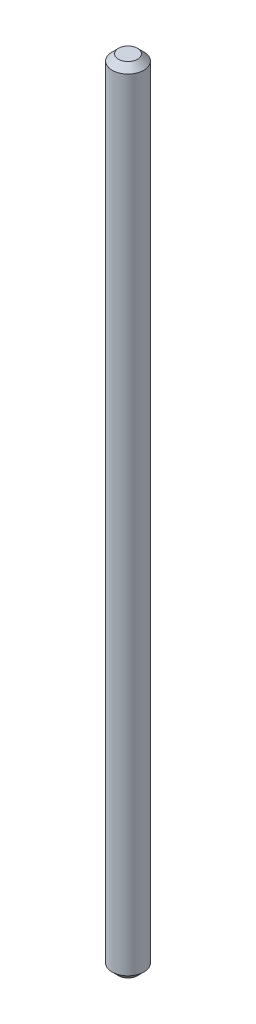
SolidWorks part; units mm, degrees
ref_plane "Front Plane" through (0, 0, 0) normal (0, 0, 1) x (1, 0, 0)
ref_plane "Top Plane" through (0, 0, 0) normal (0, 1, 0) x (1, 0, 0)
ref_plane "Right Plane" through (0, 0, 0) normal (1, 0, 0) x (0, 0, -1)
sketch "Sketch1" plane through (0, 0, 0) normal (0, 1, 0) x (1, 0, 0)
  circle A0 centre (0, 0) radius 5
  dimension "D1" = 10
extrude "Boss-Extrude1" add sketch "Sketch1" along normal blind 250
chamfer "Chamfer1" distance 2 angle 45 2 edges at (0, 0, 5) (0, 250, 5)
